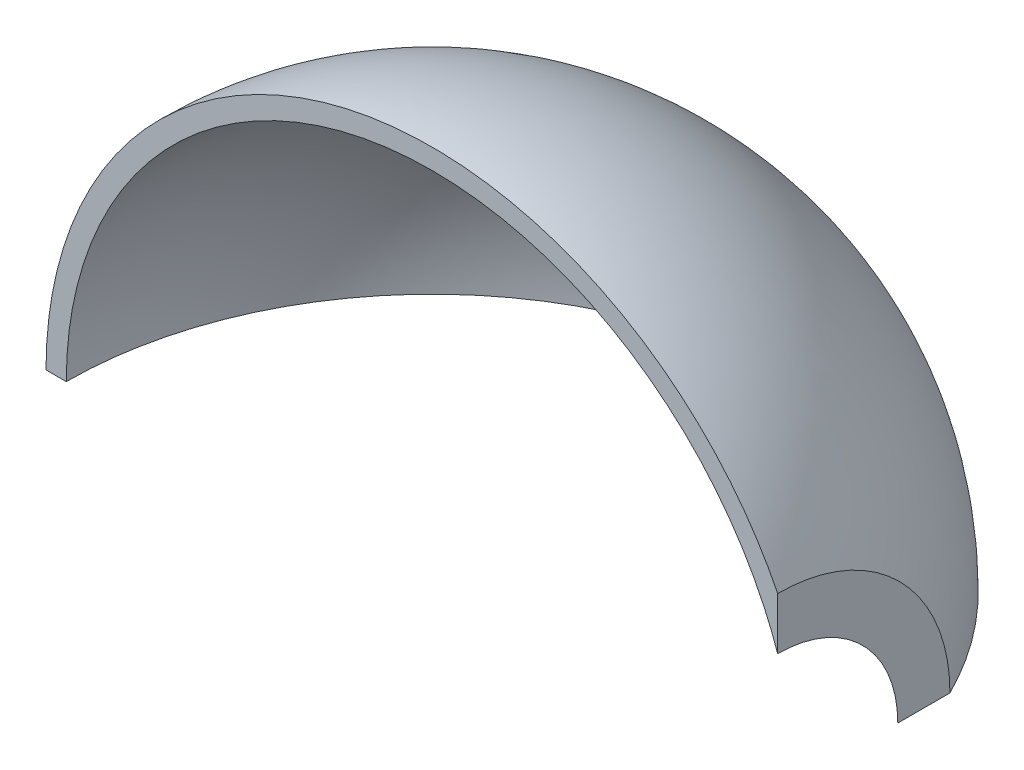
SolidWorks part; units mm, degrees
ref_plane "Front Plane" through (0, 0, 0) normal (0, 0, 1) x (1, 0, 0)
ref_plane "Top Plane" through (0, 0, 0) normal (0, 1, 0) x (1, 0, 0)
ref_plane "Right Plane" through (0, 0, 0) normal (1, 0, 0) x (0, 0, -1)
sketch "Sketch2" plane through (0, 0, 0) normal (0, 0, 1) x (1, 0, 0)
  line L4 (0, 0) -> (0, 96.2504) construction
  line L5 (-95.25, 0) -> (-90.25, 0)
  line L6 (85.25, 42.4853) -> (85.25, 29.6226)
  spline S0 degree 4 poles (-95.25, 0) (-95.25, 3.8867) (-94.8749, 10.7811) (-93.4228, 20.327) (-89.9349, 32.2051) (-85.5254, 42.5171) (-80.1052, 52.0141) (-73.6349, 60.8293) (-66.1993, 68.8473) (-57.896, 75.9629) (-48.8338, 82.0827) (-39.1314, 87.1266) (-30.193, 90.5407) (-22.2947, 92.7213) (-15.5982, 94.0302) (-10.1898, 94.7689) (-3.4253, 95.3008) (4.6926, 95.3224) (14.1068, 94.456) (24.6645, 92.2637) (34.9078, 88.8954) (43.4812, 84.9565) (50.4738, 80.9079) (56.0266, 77.108) (60.2903, 73.8222) (64.3616, 70.3009) (68.2276, 66.5554) (71.42, 63.0924) (74.013, 59.9993) (76.0749, 57.3427) (77.4652, 55.443) (78.6181, 53.7873) (79.5528, 52.3896) (80.2845, 51.2612) (81.0005, 50.1222) (81.6999, 48.974) (82.3839, 47.8143) (83.0496, 46.6487) (83.6211, 45.6137) (84.0952, 44.7315) (84.4461, 44.0633) (84.6862, 43.5989) (84.9256, 43.1305) (85.1411, 42.7042) (85.3414, 42.3028) (85.5972, 41.7822) (85.8476, 41.2657) (86.1481, 40.6365) (86.4904, 39.904) (86.8871, 39.0343) (87.3293, 38.035) (87.7591, 37.0323) (88.1779, 36.0239) (88.6866, 34.7579) (89.2739, 33.2294) (89.9249, 31.4333) (90.6217, 29.3641) (91.3922, 26.8901) (92.0729, 24.4612) (92.6694, 22.0814) (93.0836, 20.2196) (93.2783, 19.286) (93.3725, 18.8186) knots 0 0 0 0 0 0.055466 0.098387 0.137312 0.176239 0.215167 0.254094 0.293022 0.33195 0.370878 0.409805 0.448733 0.468197 0.487661 0.507125 0.526589 0.564977 0.603365 0.641754 0.680142 0.71853 0.737724 0.756918 0.776112 0.795306 0.8145 0.833694 0.843291 0.852888 0.862485 0.867284 0.872082 0.876881 0.88168 0.886478 0.891277 0.896076 0.900874 0.903273 0.905673 0.906872 0.908072 0.910471 0.912419 0.914366 0.916313 0.91826 0.922155 0.926049 0.929943 0.933838 0.937732 0.941627 0.949416 0.957204 0.964993 0.972782 0.986391 0.993195 1 1 1 1 1 construction
  spline S1 degree 4 poles (-95.25, 0) (-95.25, 3.8867) (-94.8749, 10.7811) (-93.4228, 20.327) (-89.9349, 32.2051) (-85.5254, 42.5171) (-80.1052, 52.0141) (-73.6349, 60.8293) (-66.1993, 68.8473) (-57.896, 75.9629) (-48.8338, 82.0827) (-39.1314, 87.1266) (-30.193, 90.5407) (-22.2947, 92.7213) (-15.5982, 94.0302) (-10.1898, 94.7689) (-3.4253, 95.3008) (4.6926, 95.3224) (14.1068, 94.456) (24.6645, 92.2637) (34.9078, 88.8954) (43.4812, 84.9565) (50.4738, 80.9079) (56.0266, 77.108) (60.2903, 73.8222) (64.3616, 70.3009) (68.2276, 66.5554) (71.42, 63.0924) (74.013, 59.9993) (76.0749, 57.3427) (77.4652, 55.443) (78.6181, 53.7873) (79.5528, 52.3896) (80.2845, 51.2612) (81.0005, 50.1222) (81.6999, 48.974) (82.3839, 47.8143) (83.0496, 46.6487) (83.6211, 45.6137) (84.0952, 44.7315) (84.4461, 44.0633) (84.6862, 43.5989) (84.9256, 43.1305) (85.0789, 42.8272) (85.1817, 42.6223) (85.25, 42.4853) knots 0 0 0 0 0 0.055466 0.098387 0.137312 0.176239 0.215167 0.254094 0.293022 0.33195 0.370878 0.409805 0.448733 0.468197 0.487661 0.507125 0.526589 0.564977 0.603365 0.641754 0.680142 0.71853 0.737724 0.756918 0.776112 0.795306 0.8145 0.833694 0.843291 0.852888 0.862485 0.867284 0.872082 0.876881 0.88168 0.886478 0.891277 0.896076 0.900874 0.903273 0.905673 0.906872 0.908072 0.910471 0.910471 0.910471 0.910471 0.910471
  spline S2 degree 4 poles (-90.25, 0) (-90.25, 3.7054) (-89.8841, 10.3892) (-88.4624, 19.5769) (-85.0634, 30.9525) (-80.7769, 40.7999) (-75.5955, 49.7481) (-69.4269, 58.0469) (-62.352, 65.588) (-54.4629, 72.2727) (-45.8628, 78.0138) (-36.6638, 82.7364) (-26.9862, 86.3788) (-16.9562, 88.8934) (-6.4581, 90.28) (4.3816, 90.4245) (15.4088, 89.2251) (25.0627, 86.9273) (33.0782, 84.1085) (39.5328, 81.213) (44.5414, 78.5778) (50.5835, 74.8981) (57.4463, 69.8886) (64.8077, 63.2338) (70.8172, 56.2484) (74.909, 50.4732) (77.512, 46.2633) (78.9233, 43.8122) (80.0905, 41.6298) (81.0416, 39.7339) (81.801, 38.1377) (82.3884, 36.8517) (82.9558, 35.556) (83.434, 34.4158) (83.8318, 33.4312) (84.1544, 32.6084) (84.3741, 32.0351) (84.5601, 31.5399) (84.7471, 31.0334) (84.9355, 30.5143) (85.1501, 29.9114) (85.3463, 29.3469) (85.5778, 28.6645) (85.8046, 27.9795) (86.0695, 27.1566) (86.3746, 26.1735) (86.7208, 25.0076) (87.0931, 23.6779) (87.4462, 22.3388) (87.7782, 20.9963) (88.0981, 19.6122) (88.4035, 18.1878) (88.7668, 16.347) (89.1602, 14.0854) (89.5445, 11.4346) (89.7966, 9.1527) (89.9303, 7.6282) (89.9885, 6.8653) knots 0 0 0 0 0 0.053573 0.096637 0.133928 0.171222 0.208517 0.245812 0.283106 0.320401 0.357696 0.394991 0.432286 0.46958 0.506875 0.547762 0.588649 0.629536 0.649979 0.670422 0.690866 0.711309 0.752196 0.793082 0.833969 0.84419 0.854412 0.864634 0.874856 0.879967 0.885078 0.890189 0.8953 0.900411 0.902966 0.905522 0.908077 0.909355 0.910632 0.913188 0.915743 0.918244 0.920744 0.923245 0.925745 0.930746 0.935747 0.940748 0.945749 0.950749 0.95575 0.961282 0.966813 0.977875 0.988938 1 1 1 1 1 construction
  spline S3 degree 4 poles (-90.25, 0) (-90.25, 3.7054) (-89.8841, 10.3892) (-88.4624, 19.5769) (-85.0634, 30.9525) (-80.7769, 40.7999) (-75.5955, 49.7481) (-69.4269, 58.0469) (-62.352, 65.588) (-54.4629, 72.2727) (-45.8628, 78.0138) (-36.6638, 82.7364) (-26.9862, 86.3788) (-16.9562, 88.8934) (-6.4581, 90.28) (4.3816, 90.4245) (15.4088, 89.2251) (25.0627, 86.9273) (33.0782, 84.1085) (39.5328, 81.213) (44.5414, 78.5778) (50.5835, 74.8981) (57.4463, 69.8886) (64.8077, 63.2338) (70.8172, 56.2484) (74.909, 50.4732) (77.512, 46.2633) (78.9233, 43.8122) (80.0905, 41.6298) (81.0416, 39.7339) (81.801, 38.1377) (82.3884, 36.8517) (82.9558, 35.556) (83.434, 34.4158) (83.8318, 33.4312) (84.1544, 32.6084) (84.3741, 32.0351) (84.5601, 31.5399) (84.7471, 31.0334) (84.9355, 30.5143) (85.0898, 30.081) (85.1969, 29.7755) (85.25, 29.6226) knots 0 0 0 0 0 0.053573 0.096637 0.133928 0.171222 0.208517 0.245812 0.283106 0.320401 0.357696 0.394991 0.432286 0.46958 0.506875 0.547762 0.588649 0.629536 0.649979 0.670422 0.690866 0.711309 0.752196 0.793082 0.833969 0.84419 0.854412 0.864634 0.874856 0.879967 0.885078 0.890189 0.8953 0.900411 0.902966 0.905522 0.908077 0.909355 0.910632 0.913188 0.915743 0.915743 0.915743 0.915743 0.915743
  dimension "D1" = 175.5
  dimension "D2" = 180.5
revolve "Revolve1" add sketch "Sketch2" angle 90 about L5
